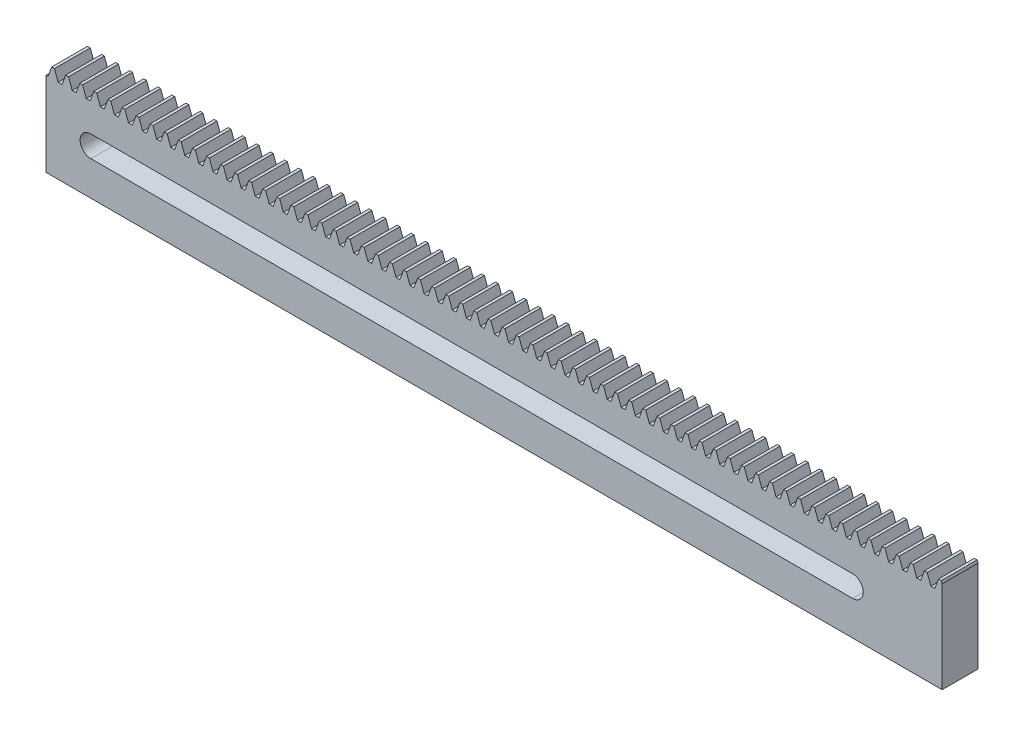
SolidWorks part; units mm, degrees
ref_plane "Plane1" through (0, 0, 0) normal (0, 0, 1) x (1, 0, 0)
ref_plane "Plane2" through (0, 0, 0) normal (0, 1, 0) x (1, 0, 0)
ref_plane "Plane3" through (0, 0, 0) normal (1, 0, 0) x (0, 0, -1)
sketch "HoldingSke" plane through (0, 0, 0) normal (0, 1, 0) x (1, 0, 0)
  line L0 (0, 0) -> (0.0928, 0.6602)
  line L1 (-15, 0) -> (100, 0) construction
  line L2 (0, 0) -> (-2.1039, 2.3779)
  line L3 (0, 0) -> (-11.863, 4.5341)
  line L4 (0, 0) -> (3.6497, 7.8269)
  line L5 (0, 0) -> (-23.7986, -8.8762)
  line L6 (0, 0) -> (-10.5278, -7.1032)
  line L9 (-71.009, 38.7566) -> (210.8988, 141.3627)
  line L10 (-76.2, 3.8779) -> (-46.2, 3.8779)
  line L11 (0, 0) -> (-12, 0)
  line L12 (-76.2, 101.6) -> (-76.147, 101.6)
  line L13 (24.9733, 27.94) -> (52.9518, 28.4284)
  line L14 (24.9733, 27.94) -> (24.9743, 27.94)
  line L15 (24.9733, 27.94) -> (100.4006, 29.5858)
  circle A0 centre (0, 0) radius 19.05
  circle A1 centre (0, 0) radius 15
  circle A2 centre (0, 0) radius 12.7
  dimension "MPH" = 30
  dimension "Diameter" = 38.1
  dimension "Num_teeth" = 65
  dimension "Pitch" = 0.6667
  dimension "Width" = 12
  dimension "Show_teeth" = 998
  dimension "Thickness" = 12.7
  dimension "Ap" = 20
  dimension "Pitch_height" = 30
  dimension "Backlash" = 0.053
  dimension "Addendum_fac" = 1
  dimension "Dedendum_fac" = 1.25
  dimension "Clearance_fac" = 0.25
  dimension "Dedendum_add" = 0.001
  dimension "Length" = 300
  dimension "Module" = 1.5
sketch "BlankSke" plane through (0, 0, 0) normal (0, 0, 1) x (1, 0, 0)
  line L1 (0, 0) -> (300, 0)
  line L2 (0, 0) -> (0, 31.5)
  line L3 (0, 31.5) -> (300, 31.5)
  line L4 (300, 0) -> (300, 31.5)
  dimension "Length" = 300
  dimension "Blank_height" = 31.5
extrude "Blank" add sketch "BlankSke" against normal blind 12
sketch "TooCutSkeIll" plane through (0, 0, 0) normal (0, 0, 1) x (1, 0, 0)
  line L0 (-1.8687, 31.4605) -> (-0.7447, 28.3724)
  line L1 (-0.3914, 28.125) -> (0.3914, 28.125)
  line L2 (0.7447, 28.3724) -> (1.8687, 31.4605)
  line L3 (300, 31.5) -> (0, 31.5) construction
  line L4 (0, 0) -> (0, 64.897) construction
  line L5 (-13.208, 30) -> (12.954, 30) construction
  line L6 (0, 0) -> (300, 0) construction
  line L7 (1.3371, 30) -> (1.3371, 48.7463) construction
  line L8 (-1.3371, 30) -> (-1.3371, 48.7463) construction
  line L9 (1.9251, 31.5) -> (1.9251, 31.5254)
  line L10 (-1.9251, 31.5) -> (-1.9251, 31.5254)
  line L11 (-1.9251, 31.5254) -> (1.9251, 31.5254)
  arc A0 (0.3914, 28.125) -> (0.7447, 28.3724) centre (0.3914, 28.501) ccw
  arc A1 (-0.7447, 28.3724) -> (-0.3914, 28.125) centre (-0.3914, 28.501) ccw
  arc A2 (1.9251, 31.5) -> (1.8687, 31.4605) centre (1.9251, 31.44) ccw
  arc A3 (-1.8687, 31.4605) -> (-1.9251, 31.5) centre (-1.9251, 31.44) ccw
  dimension "Root_fillet" = 0.376
  dimension "Break_rad" = 0.06
  dimension "Pitch_height" = 30
  dimension "Gap_width" = 2.6742
  dimension "Dedendum" = 1.875
  dimension "Addendum_plus" = 1.5254
  dimension "Pressure_angle" = 20
extrude "ToothCutIll" [suppressed] cut sketch "TooCutSkeIll" against normal through all
sketch "TooCutSkeSim" plane through (0, 0, 0) normal (0, 0, 1) x (1, 0, 0)
  line L0 (0.6547, 28.125) -> (-0.6547, 28.125)
  line L1 (1.8923, 31.5254) -> (0.6547, 28.125)
  line L2 (0, 17.4625) -> (0, 53.467) construction
  line L3 (1.8923, 31.5254) -> (-1.8923, 31.5254)
  line L6 (-1.8923, 31.5254) -> (-0.6547, 28.125)
  line L9 (-1.3371, 30) -> (1.3371, 30) construction
  line L10 (0, 0) -> (300, 0) construction
  line L11 (1.3371, 30) -> (1.3371, 53.467) construction
  line L12 (-1.3371, 30) -> (-1.3371, 53.467) construction
  dimension "Pitch_height" = 30
  dimension "Pressure_angle" = 20
  dimension "Gap_width" = 2.6742
  dimension "Dedendum" = 1.875
  dimension "Addendum_plus" = 1.5254
extrude "ToothCutSim" cut sketch "TooCutSkeSim" against normal through all
pattern_linear "TeethCuts" count 64 spacing 4.7124 along (1, 0, 0) of "ToothCutIll", "ToothCutSim"
sketch "Sketch1" plane through (0, 0, 0) normal (0, 0, 1) x (1, 0, 0)
  line L0 (15, 15.0732) -> (270, 15.0732) construction
  line L1 (15, 18.6605) -> (270, 18.6605)
  line L2 (15, 11.4859) -> (270, 11.4859)
  line L3 (0, 28.125) -> (0, 0) construction
  line L4 (300, 0) -> (300, 30.7028) construction
  arc A0 (15, 18.6605) -> (15, 11.4859) centre (15, 15.0732) ccw
  arc A1 (270, 11.4859) -> (270, 18.6605) centre (270, 15.0732) ccw
  point P2 (142.5, 15.0732)
  point P7 (0, 14.0625)
  dimension "D1" = 7.1746
  dimension "D2" = 15
  dimension "D3" = 30
extrude "Cut-Extrude2" cut sketch "Sketch1" against normal through all
equation "' \"Module@HoldingSke\" = 6.35"
equation "' \"Num_teeth@HoldingSke\" = 12"
equation "' \"Ap@HoldingSke\" =  20"
equation "' \"Width@HoldingSke\" = 0.25 * 25.4"
equation "' \"Show_teeth@HoldingSke\" = 500"
equation "' \"Backlash@HoldingSke\" = 0.009 * 25.4"
equation "' \"Addendum_fac@HoldingSke\" = 1.0"
equation "' \"Dedendum_fac@HoldingSke\" = 1.25"
equation "' \"Dedendum_add@HoldingSke\" = 0.00005 * 25.4"
equation "' \"Clearance_fac@HoldingSke\" = 0.25"
equation "' \"Pitch_height@HoldingSke\" = 1 * 25.4"
equation "' \"Length@HoldingSke\" = 4.71 * 25.4"
equation "\"Pitch@HoldingSke\" = 1 / \"Module@HoldingSke\""
equation "\"MPH@HoldingSke\" = \"Dedendum_fac@HoldingSke\" / \"Pitch@HoldingSke\" + 2 * \"Dedendum_add@HoldingSke\" + 0.002 * 25.4"
equation "\"MPH@HoldingSke\" = ((sgn( \"MPH@HoldingSke\" - \"Pitch_height@HoldingSke\")+1)*( \"MPH@HoldingSke\" - \"Pitch_height@HoldingSke\"))/2 + \"Pitch_height@HoldingSke\""
equation "\"Blank_height@BlankSke\" = \"Pitch_height@HoldingSke\" + \"Addendum_fac@HoldingSke\"  / \"Pitch@HoldingSke\" "
equation "\"Length@BlankSke\" =  \"Length@HoldingSke\""
equation "\"Face_width@Blank\" = \"Width@HoldingSke\""
equation "\"Pressure_angle@TooCutSkeIll\" = \"Ap@HoldingSke\""
equation "\"Addendum_plus@TooCutSkeIll\" =  \"Addendum_fac@HoldingSke\"  / \"Pitch@HoldingSke\" + 0.001 *25.4"
equation "\"Dedendum@TooCutSkeIll\" = \"Dedendum_fac@HoldingSke\"  / \"Pitch@HoldingSke\""
equation "\"Pitch_height@TooCutSkeIll\" =  \"MPH@HoldingSke\""
equation "\"Gap_width@TooCutSkeIll\" = 3.14159265 / 2 / \"Pitch@HoldingSke\" + 6 * \"Backlash@HoldingSke\""
equation "\"Pressure_angle@TooCutSkeSim\" = \"Ap@HoldingSke\""
equation "\"Addendum_plus@TooCutSkeSim\" =  \"Addendum_fac@HoldingSke\"  / \"Pitch@HoldingSke\" + 0.001 * 25.4"
equation "\"Dedendum@TooCutSkeSim\" = \"Dedendum_fac@HoldingSke\"  / \"Pitch@HoldingSke\""
equation "\"Pitch_height@TooCutSkeSim\" =  \"MPH@HoldingSke\""
equation "\"Gap_width@TooCutSkeSim\" = 3.14159265 / 2 / \"Pitch@HoldingSke\" + 6 * \"Backlash@HoldingSke\""
equation "\"Root_fillet@TooCutSkeIll\" = \"Clearance_fac@HoldingSke\" / \"Pitch@HoldingSke\" + \"Dedendum_add@HoldingSke\""
equation "\"Break_rad@TooCutSkeIll\" = 0.02 / \"Pitch@HoldingSke\" * 2"
equation "\"Linear_pitch@TeethCuts\" = 3.14159265 / \"Pitch@HoldingSke\""
equation "\"Num_teeth@HoldingSke\" = int( ( \"Length@HoldingSke\" + 0 ) / (3.14159265 / \"Pitch@HoldingSke\")) + 0.9999  + 1"
equation " \"Num_teeth@TeethCuts\" = int( \"Show_teeth@HoldingSke\" ) + 1"
equation " \"Num_teeth@TeethCuts\" = ((sgn( \"Num_teeth@TeethCuts\" - \"Num_teeth@HoldingSke\" )-1)*( \"Num_teeth@TeethCuts\" - \"Num_teeth@HoldingSke\" ))/-2+ \"Num_teeth@HoldingSke\""
equation " \"Num_teeth@TeethCuts\" = ((sgn( \"Num_teeth@TeethCuts\" - 2.0)+1)*( \"Num_teeth@TeethCuts\" - 2.0))/2 +2.0"
